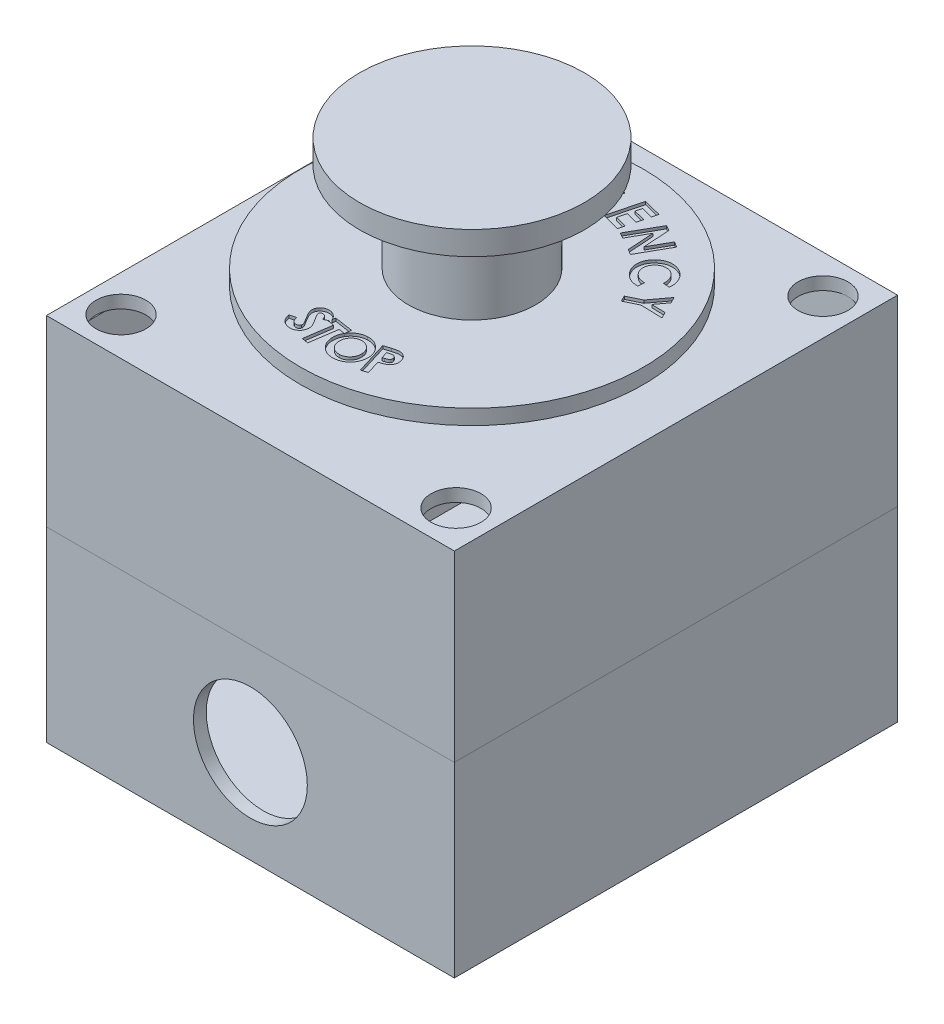
SolidWorks part; units mm, degrees
ref_plane "Front Plane" through (0, 0, 0) normal (0, 0, 1) x (1, 0, 0)
ref_plane "Top Plane" through (0, 0, 0) normal (0, 1, 0) x (1, 0, 0)
ref_plane "Right Plane" through (0, 0, 0) normal (1, 0, 0) x (0, 0, -1)
sketch "Sketch1" plane through (0, 0, 0) normal (0, 1, 0) x (1, 0, 0)
  line L1 (35.825, -38.925) -> (-35.825, -38.925)
  line L2 (35.825, -38.925) -> (35.825, 38.925)
  line L3 (35.825, 38.925) -> (-35.825, 38.925)
  line L4 (-35.825, -38.925) -> (-35.825, 38.925)
  line L5 (35.825, -38.925) -> (-35.825, 38.925) construction
  line L6 (35.825, 38.925) -> (-35.825, -38.925) construction
  point P0 (0, 0)
  dimension "D1" = 71.65
  dimension "D2" = 77.85
extrude "Boss-Extrude1" add sketch "Sketch1" along normal blind 32.8
shell "Shell3" thickness 2.25
sketch "Sketch2" plane through (0, 32.8, 0) normal (0, 1, 0) x (1, 0, 0)
  line L1 (35.825, -38.925) -> (-35.825, -38.925)
  line L2 (35.825, -38.925) -> (35.825, 38.925)
  line L3 (35.825, 38.925) -> (-35.825, 38.925)
  line L4 (-35.825, -38.925) -> (-35.825, 38.925)
  line L5 (35.825, -38.925) -> (-35.825, 38.925) construction
  line L6 (35.825, 38.925) -> (-35.825, -38.925) construction
  point P0 (0, 0)
extrude "Boss-Extrude2" add sketch "Sketch2" along normal blind 32.15 separate body
shell "Shell4" thickness 2.25
sketch "Sketch3" plane through (0, 64.95, 0) normal (0, 1, 0) x (1, 0, 0)
  line L1 (29.425, -32.225) -> (-29.425, -32.225) construction
  line L2 (29.425, -32.225) -> (29.425, 32.225) construction
  line L3 (29.425, 32.225) -> (-29.425, 32.225) construction
  line L4 (-29.425, -32.225) -> (-29.425, 32.225) construction
  line L5 (29.425, -32.225) -> (-29.425, 32.225) construction
  line L6 (29.425, 32.225) -> (-29.425, -32.225) construction
  circle A0 centre (0, 0) radius 11.175
  circle A1 centre (-29.425, 32.225) radius 4.375
  circle A2 centre (29.425, 32.225) radius 4.375
  circle A3 centre (29.425, -32.225) radius 4.375
  circle A4 centre (-29.425, -32.225) radius 4.375
  dimension "D1" = 22.35
  dimension "D4" = 8.75
  dimension "D2" = 64.45
  dimension "D3" = 58.85
extrude "Cut-Extrude1" cut sketch "Sketch3" against normal blind 2.25
ref_plane "Plane1" through (0, 67.95, 0) normal (0, 1, 0) x (1, 0, 0)
sketch "Sketch4" plane through (0, 67.95, 0) normal (0, 1, 0) x (1, 0, 0)
  circle A0 centre (0, 0) radius 11.175
  circle A1 centre (0, 0) radius 30.125
  dimension "D1" = 22.35
  dimension "D2" = 18.95
extrude "Boss-Extrude3" add sketch "Sketch4" along normal blind 2.65 separate body
sketch "Sketch5" plane through (0, 70.6, 0) normal (0, 1, 0) x (1, 0, 0)
  line L0 (-20, 0) -> (20, 0) construction
  arc A0 (20, 0) -> (-20, 0) centre (0, 0) ccw construction
  arc A1 (-26, 0) -> (26, 0) centre (0, 0) ccw construction
  text T0 "EMERGENCY" font "Century Gothic" height 6
  text T1 "STOP" font "Century Gothic" height 6
  dimension "D1" = 20
  dimension "D2" = 26
extrude "Cut-Extrude2" cut sketch "Sketch5" against normal blind 0.5
sketch "Sketch6" plane through (0, 64.95, 0) normal (0, 1, 0) x (1, 0, 0)
  circle A0 centre (0, 0) radius 11.175
extrude "Boss-Extrude4" add sketch "Sketch6" along normal blind 21.35
sketch "Sketch7" plane through (0, 86.3, 0) normal (0, 1, 0) x (1, 0, 0)
  circle A0 centre (0, 0) radius 19.75
  dimension "D1" = 39.5
extrude "Boss-Extrude5" add sketch "Sketch7" along normal blind 4.15
sketch "Sketch8" plane through (0, 0, 38.925) normal (0, 0, 1) x (1, 0, 0)
  line L0 (0, 0) -> (0, 32.8) construction
  line L1 (-35.825, 0) -> (35.825, 0) construction
  line L2 (-35.825, 32.8) -> (35.825, 32.8) construction
  circle A0 centre (0, 16.4) radius 10
  point P8 (0, 16.4)
  dimension "D1" = 20
extrude "Cut-Extrude3" cut sketch "Sketch8" against normal up to next (2.25 mm away)
